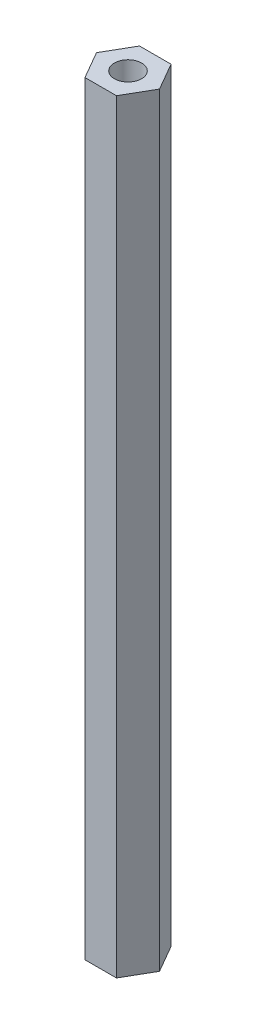
SolidWorks part; units mm, degrees
ref_plane "Front Plane" through (0, 0, 0) normal (0, 0, 1) x (1, 0, 0)
ref_plane "Top Plane" through (0, 0, 0) normal (0, 1, 0) x (1, 0, 0)
ref_plane "Right Plane" through (0, 0, 0) normal (1, 0, 0) x (0, 0, -1)
sketch "Sketch1" plane through (0, 0, 0) normal (0, 1, 0) x (1, 0, 0)
  line L1 (1.8331, 3.175) -> (-1.8331, 3.175)
  line L2 (-1.8331, 3.175) -> (-3.6662, 0)
  line L3 (-3.6662, 0) -> (-1.8331, -3.175)
  line L4 (-1.8331, -3.175) -> (1.8331, -3.175)
  line L5 (1.8331, -3.175) -> (3.6662, 0)
  line L6 (3.6662, 0) -> (1.8331, 3.175)
  circle A0 centre (0, 0) radius 3.175 construction
  circle A1 centre (0, 0) radius 1.5875
  dimension "D2" = 3.175
  dimension "D1" = 6.35
extrude "Boss-Extrude1" add sketch "Sketch1" along normal blind 88.9
